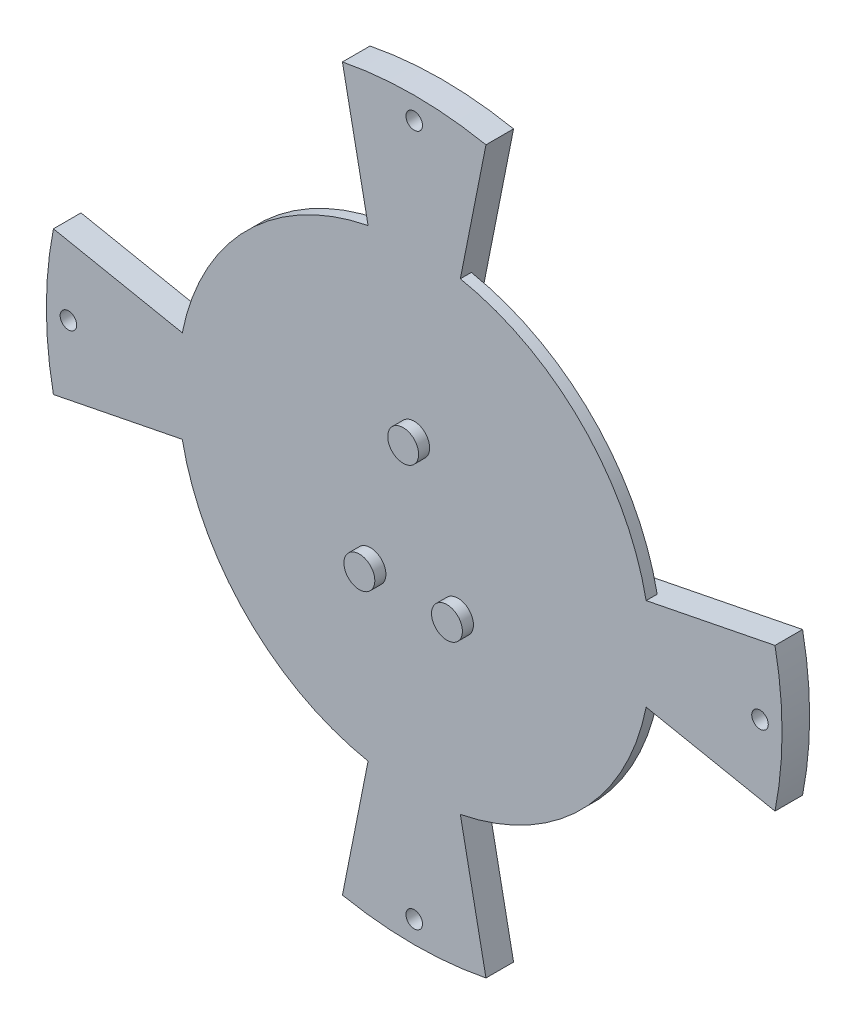
SolidWorks part; units mm, degrees
ref_plane "Front" through (0, 0, 0) normal (0, 0, 1) x (1, 0, 0)
ref_plane "Top" through (0, 0, 0) normal (0, 1, 0) x (1, 0, 0)
ref_plane "Right" through (0, 0, 0) normal (1, 0, 0) x (0, 0, -1)
sketch "Sketch1" plane through (0, 0, 0) normal (0, 0, 1) x (1, 0, 0)
  circle A0 centre (0, 0) radius 25
extrude "Extrude1" add sketch "Sketch1" along normal blind 5
sketch "Sketch4" plane through (0, 0, 5) normal (0, 0, 1) x (1, 0, 0)
  line L0 (4.044, 20.331) -> (-4.044, -20.331) construction
  line L1 (-4.044, 20.331) -> (4.044, -20.331) construction
  line L2 (-20.331, 4.044) -> (20.331, -4.044) construction
  line L3 (20.331, 4.044) -> (-20.331, -4.044) construction
  line L4 (-13.0074, 65.3939) -> (-4.6821, 23.5389)
  line L5 (13.0074, 65.3939) -> (4.6821, 23.5389)
  line L6 (65.3939, 13.0074) -> (23.5389, 4.6821)
  line L7 (65.3939, -13.0074) -> (23.5389, -4.6821)
  line L8 (4.6821, -23.5389) -> (13.0074, -65.3939)
  line L9 (-13.0074, -65.3939) -> (-4.6821, -23.5389)
  line L10 (-23.5389, -4.6821) -> (-65.3939, -13.0074)
  line L11 (-65.3939, 13.0074) -> (-23.5389, 4.6821)
  circle A0 centre (0, 20.73) radius 0.7 construction
  circle A1 centre (0, -20.73) radius 0.7 construction
  circle A2 centre (20.73, 0) radius 0.7 construction
  circle A3 centre (-20.73, 0) radius 0.7 construction
  circle A4 centre (-14.658, 14.658) radius 0.7 construction
  circle A5 centre (14.658, 14.658) radius 0.7 construction
  circle A6 centre (14.658, -14.658) radius 0.7 construction
  circle A7 centre (-14.658, -14.658) radius 0.7 construction
  circle A8 centre (19.152, 7.933) radius 0.7 construction
  circle A9 centre (7.933, 19.152) radius 0.7 construction
  circle A10 centre (19.152, -7.933) radius 0.7 construction
  circle A11 centre (7.933, -19.152) radius 0.7 construction
  circle A12 centre (-7.933, 19.152) radius 0.7 construction
  circle A13 centre (-19.152, 7.933) radius 0.7 construction
  circle A14 centre (-19.152, -7.933) radius 0.7 construction
  circle A15 centre (-7.933, -19.152) radius 0.7 construction
  circle A16 centre (20.331, 4.044) radius 0.7 construction
  circle A17 centre (20.331, -4.044) radius 0.7 construction
  circle A18 centre (4.044, -20.331) radius 0.7 construction
  circle A19 centre (-4.044, -20.331) radius 0.7 construction
  circle A20 centre (4.044, 20.331) radius 0.7 construction
  circle A21 centre (-4.044, 20.331) radius 0.6677 construction
  circle A22 centre (-20.331, 4.044) radius 0.7 construction
  circle A23 centre (-20.331, -4.044) radius 0.7 construction
  circle A24 centre (17.236, 11.516) radius 0.7 construction
  circle A25 centre (11.516, 17.236) radius 0.7 construction
  circle A26 centre (17.236, -11.516) radius 0.7 construction
  circle A27 centre (11.516, -17.236) radius 0.7 construction
  circle A28 centre (-11.516, -17.236) radius 0.7 construction
  circle A29 centre (-17.236, -11.516) radius 0.7 construction
  circle A30 centre (-17.236, 11.516) radius 0.7 construction
  circle A31 centre (-11.516, 17.236) radius 0.7 construction
  circle A32 centre (0, 17.555) radius 0.7 construction
  circle A33 centre (17.555, 0) radius 0.7 construction
  circle A34 centre (0, -17.555) radius 0.7 construction
  circle A35 centre (-17.555, 0) radius 0.7 construction
  circle A36 centre (-12.413, 12.413) radius 0.7 construction
  circle A37 centre (12.413, 12.413) radius 0.7 construction
  circle A38 centre (12.413, -12.413) radius 0.7 construction
  circle A39 centre (-12.413, -12.413) radius 0.7 construction
  circle A40 centre (-16.218, 6.718) radius 0.7 construction
  circle A41 centre (16.218, 6.718) radius 0.7 construction
  circle A42 centre (16.218, -6.718) radius 0.7 construction
  circle A43 centre (-16.218, -6.718) radius 0.7 construction
  circle A44 centre (6.718, 16.218) radius 0.7 construction
  circle A45 centre (6.718, -16.218) radius 0.7 construction
  circle A46 centre (-6.718, -16.218) radius 0.7 construction
  circle A47 centre (-6.718, 16.218) radius 0.7 construction
  circle A48 centre (0, 0) radius 60 construction
  circle A49 centre (0, 0) radius 66.675 construction
  circle A50 centre (0, 0) radius 24 construction
  arc A51 (23.5389, 4.6821) -> (23.5389, -4.6821) centre (0, 0) cw
  arc A52 (65.3939, 13.0074) -> (65.3939, -13.0074) centre (0, 0) cw
  arc A53 (4.6821, -23.5389) -> (-4.6821, -23.5389) centre (0, 0) cw
  arc A54 (13.0074, -65.3939) -> (-13.0074, -65.3939) centre (0, 0) cw
  arc A55 (-23.5389, -4.6821) -> (-23.5389, 4.6821) centre (0, 0) cw
  arc A56 (-65.3939, -13.0074) -> (-65.3939, 13.0074) centre (0, 0) cw
  arc A57 (-4.6821, 23.5389) -> (4.6821, 23.5389) centre (0, 0) cw
  arc A58 (-13.0074, 65.3939) -> (13.0074, 65.3939) centre (0, 0) cw
  circle A59 centre (62.675, 0) radius 1.5
  circle A60 centre (0, 62.675) radius 1.5
  circle A61 centre (0, -62.675) radius 1.5
  circle A62 centre (-62.675, 0) radius 1.5
  point P125 (-62.675, 0)
  point P126 (0, 62.675)
  point P127 (62.675, 0)
  point P128 (0, -62.675)
extrude "Extrude2" add sketch "Sketch4" against normal blind 5
sketch "Sketch6" plane through (0, 0, 5) normal (0, 0, 1) x (1, 0, 0)
  circle A0 centre (-7.9375, -11.1125) radius 2.8
  circle A1 centre (7.9375, -11.1125) radius 2.8
  circle A2 centre (0, 12.7) radius 2.8
extrude "Extrude4" add sketch "Sketch6" along normal blind 2
sketch "Sketch7" plane through (0, 0, 5) normal (0, 0, 1) x (1, 0, 0)
  circle A0 centre (0, 0) radius 23.8125
  circle A1 centre (0, 0) radius 42.8625
extrude "Extrude5" add sketch "Sketch7" against normal blind 2
